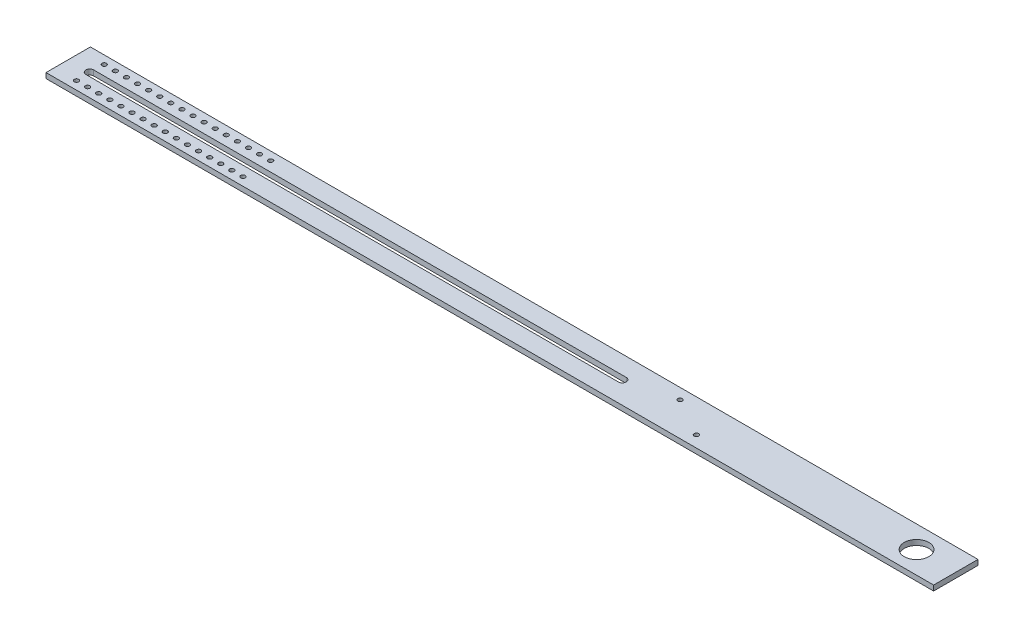
SolidWorks part; units mm, degrees
ref_plane "Front Plane" through (0, 0, 0) normal (0, 0, 1) x (1, 0, 0)
ref_plane "Top Plane" through (0, 0, 0) normal (0, 1, 0) x (1, 0, 0)
ref_plane "Right Plane" through (0, 0, 0) normal (1, 0, 0) x (0, 0, -1)
sketch "Sketch1" plane through (0, 0, 0) normal (0, 1, 0) x (1, 0, 0)
  line L1 (0, 0) -> (1016, 0)
  line L2 (0, 0) -> (0, 50.8)
  line L3 (0, 50.8) -> (1016, 50.8)
  line L4 (1016, 0) -> (1016, 50.8)
  dimension "D1" = 1016
  dimension "D2" = 50.8
extrude "Boss-Extrude1" add sketch "Sketch1" along normal blind 6
sketch "Sketch2" plane through (0, 6, 0) normal (0, 1, 0) x (1, 0, 0)
  line L0 (24.7, 25.4) -> (634.3, 25.4) construction
  line L1 (24.7, 29.9) -> (634.3, 29.9)
  line L2 (24.7, 20.9) -> (634.3, 20.9)
  line L3 (20.2, 50.8) -> (20.2, 0) construction
  line L4 (1016, 50.8) -> (0, 50.8) construction
  line L5 (0, 0) -> (1016, 0) construction
  line L6 (0, 50.8) -> (0, 0) construction
  arc A0 (24.7, 29.9) -> (24.7, 20.9) centre (24.7, 25.4) ccw
  arc A1 (634.3, 20.9) -> (634.3, 29.9) centre (634.3, 25.4) ccw
  point P2 (329.5, 25.4)
  point P13 (20.2, 25.4)
  dimension "D2" = 4.5
  dimension "D1" = 20.2
  dimension "D3" = 609.6
  dimension "D4" = 25.4
extrude "Cut-Extrude1" cut sketch "Sketch2" against normal blind 6
sketch "Sketch3" plane through (0, 6, 0) normal (0, 1, 0) x (1, 0, 0)
  line L0 (1016, 0) -> (1016, 50.8) construction
  line L1 (1016, 50.8) -> (0, 50.8) construction
  circle A0 centre (971.042, 25.4) radius 14.097
  dimension "D1" = 28.194
  dimension "D2" = 44.958
  dimension "D3" = 25.4
extrude "Cut-Extrude2" cut sketch "Sketch3" against normal through all
hole_wizard "1/4-20 Tapped Hole1" positions "Sketch4" profile "Sketch5" tap size "1/4-20" standard "ANSI Inch" end condition through all
sketch "Sketch4" plane through (0, 6, 0) normal (0, 1, 0) x (1, 0, 0)
  line L0 (0, 50.8) -> (0, 0) construction
  line L1 (1016, 50.8) -> (0, 50.8) construction
  point P0 (25.4, 41.275)
  dimension "D1" = 25.4
  dimension "D2" = 9.525
sketch "Sketch5" plane through (25.4, 6, -41.275) normal (1, 0, 0) x (0, 0, 1)
  line L0 (0, 0) -> (0, 6)
  line L1 (0, 6) -> (2.5527, 6)
  line L2 (2.5527, 6) -> (2.5527, 0)
  line L5 (2.5527, 0) -> (0, 0)
  line L11 (0, -6.35) -> (0, 107.95) construction
  dimension "Thru Tap Drill Dia." = 5.1054
  dimension "Thru Tap Drill Depth" = 6
cosmetic thread "Hole Thread1" parameters "D2"=6.35
pattern_linear "LPattern1" count 16 spacing 12.7 along (1, 0, 0) count 2 spacing 31.75 along (0, 0, 1) of "1/4-20 Tapped Hole1"
cosmetic thread "Hole Thread2" parameters "D2"=6.35
cosmetic thread "Hole Thread3" parameters "D2"=6.35
cosmetic thread "Hole Thread4" parameters "D2"=6.35
cosmetic thread "Hole Thread5" parameters "D2"=6.35
cosmetic thread "Hole Thread6" parameters "D2"=6.35
cosmetic thread "Hole Thread7" parameters "D2"=6.35
cosmetic thread "Hole Thread8" parameters "D2"=6.35
cosmetic thread "Hole Thread9" parameters "D2"=6.35
cosmetic thread "Hole Thread10" parameters "D2"=6.35
cosmetic thread "Hole Thread11" parameters "D2"=6.35
cosmetic thread "Hole Thread12" parameters "D2"=6.35
cosmetic thread "Hole Thread13" parameters "D2"=6.35
cosmetic thread "Hole Thread14" parameters "D2"=6.35
cosmetic thread "Hole Thread15" parameters "D2"=6.35
cosmetic thread "Hole Thread16" parameters "D2"=6.35
cosmetic thread "Hole Thread17" parameters "D2"=6.35
cosmetic thread "Hole Thread18" parameters "D2"=6.35
cosmetic thread "Hole Thread19" parameters "D2"=6.35
cosmetic thread "Hole Thread20" parameters "D2"=6.35
cosmetic thread "Hole Thread21" parameters "D2"=6.35
cosmetic thread "Hole Thread22" parameters "D2"=6.35
cosmetic thread "Hole Thread23" parameters "D2"=6.35
cosmetic thread "Hole Thread24" parameters "D2"=6.35
cosmetic thread "Hole Thread25" parameters "D2"=6.35
cosmetic thread "Hole Thread26" parameters "D2"=6.35
cosmetic thread "Hole Thread27" parameters "D2"=6.35
cosmetic thread "Hole Thread28" parameters "D2"=6.35
cosmetic thread "Hole Thread29" parameters "D2"=6.35
cosmetic thread "Hole Thread30" parameters "D2"=6.35
cosmetic thread "Hole Thread31" parameters "D2"=6.35
cosmetic thread "Hole Thread32" parameters "D2"=6.35
hole_wizard "1/4-20 Tapped Hole2" positions "Sketch6" profile "Sketch7" tap size "1/4-20" standard "ANSI Inch" end condition through all
sketch "Sketch6" plane through (0, 6, 0) normal (0, 1, 0) x (1, 0, 0)
  line L0 (687.3184, 38.4906) -> (731.3125, 13.0906) construction
  line L2 (1016, 50.8) -> (0, 50.8) construction
  line L3 (634.3, 25.4) -> (653.223, 58.1756)
  line L6 (653.223, 58.1756) -> (687.3184, 38.4906)
  point P0 (687.3184, 38.4906)
  point P2 (731.3125, 13.0906)
  dimension "D1" = 30
  dimension "D2" = 37.846
  dimension "D3" = 39.37
  dimension "D4" = 90
  dimension "D5" = 90
  dimension "D6" = 90.17
sketch "Sketch7" plane through (687.3184, 6, -38.4906) normal (1, 0, 0) x (0, 0, 1)
  line L0 (0, 0) -> (0, 6)
  line L1 (0, 6) -> (2.5527, 6)
  line L2 (2.5527, 6) -> (2.5527, 0)
  line L5 (2.5527, 0) -> (0, 0)
  line L11 (0, -6.35) -> (0, 107.95) construction
  dimension "Thru Tap Drill Dia." = 5.1054
  dimension "Thru Tap Drill Depth" = 6
cosmetic thread "Hole Thread33" parameters "D2"=6.35
cosmetic thread "Hole Thread34" parameters "D2"=6.35
